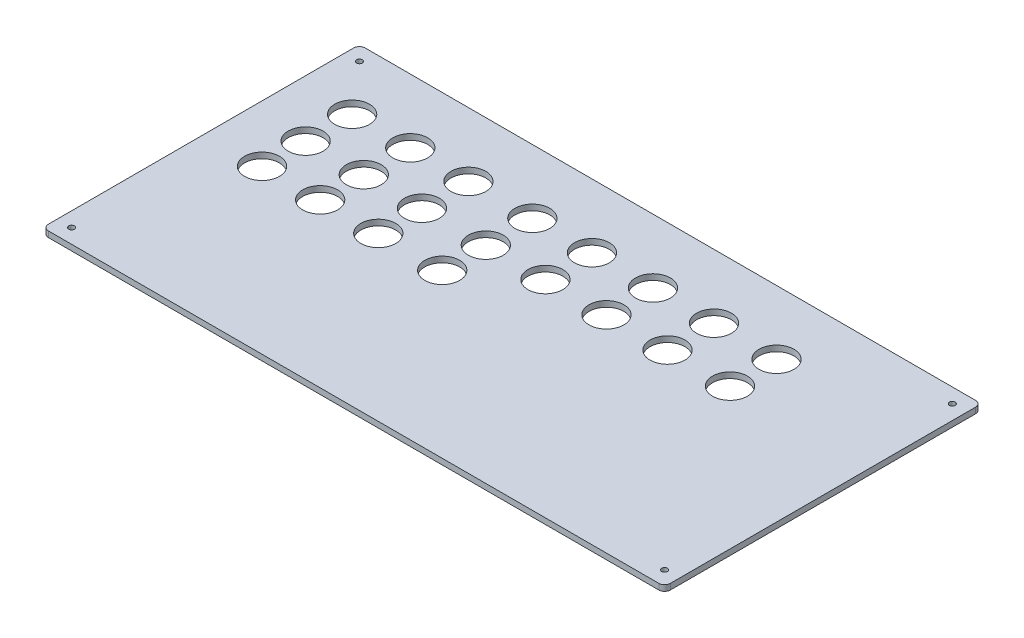
SolidWorks part; units mm, degrees
ref_plane "Front Plane" through (0, 0, 0) normal (0, 0, 1) x (1, 0, 0)
ref_plane "Top Plane" through (0, 0, 0) normal (0, 1, 0) x (1, 0, 0)
ref_plane "Right Plane" through (0, 0, 0) normal (1, 0, 0) x (0, 0, -1)
sketch "Sketch2" plane through (0, 0, 0) normal (0, 1, 0) x (1, 0, 0)
  line L1 (105, 54.5) -> (-105, 54.5)
  line L2 (107, 52.5) -> (107, -52.5)
  line L3 (105, -54.5) -> (-105, -54.5)
  line L4 (-107, 52.5) -> (-107, -52.5)
  line L5 (107, 54.5) -> (-107, -54.5) construction
  line L6 (107, -54.5) -> (-107, 54.5) construction
  arc A0 (105, 54.5) -> (107, 52.5) centre (105, 52.5) cw
  arc A1 (107, -52.5) -> (105, -54.5) centre (105, -52.5) cw
  arc A2 (-105, -54.5) -> (-107, -52.5) centre (-105, -52.5) cw
  arc A3 (-105, 54.5) -> (-107, 52.5) centre (-105, 52.5) ccw
  point P0 (0, 0)
  dimension "D3" = 2
  dimension "D1" = 214
  dimension "D2" = 109
extrude "Boss-Extrude1" add sketch "Sketch2" along normal blind 2
sketch "Sketch3" plane through (0, 2, 0) normal (0, 1, 0) x (1, 0, 0)
  line L0 (-107, 52.5) -> (-107, -52.5) construction
  line L1 (105, 54.5) -> (-105, 54.5) construction
  circle A0 centre (-87.5, 32.5) radius 6
  circle A1 centre (-67.5, 32.5) radius 6
  circle A2 centre (-47.5, 32.5) radius 6
  circle A3 centre (-25.5, 32.5) radius 6
  circle A4 centre (-5, 32.5) radius 6
  circle A5 centre (16, 32.5) radius 6
  circle A6 centre (37, 32.5) radius 6
  circle A7 centre (58.5, 32.5) radius 6
  circle A8 centre (-87.5, 16.5) radius 6
  circle A9 centre (-67.5, 16.5) radius 6
  circle A10 centre (-47.5, 16.5) radius 6
  circle A11 centre (-25.5, 16.5) radius 6
  circle A12 centre (-5, 16.5) radius 6
  circle A13 centre (16, 16.5) radius 6
  circle A14 centre (37, 16.5) radius 6
  circle A15 centre (58.5, 16.5) radius 6
  circle A16 centre (-67.5, 1.5) radius 6
  circle A17 centre (-87.5, 1.5) radius 6
  circle A18 centre (-47.5, 1.5) radius 6
  circle A19 centre (-25.5, 1.5) radius 6
  dimension "D3" = 12
  dimension "D8" = 2
  dimension "D1" = 19.5
  dimension "D2" = 22
  dimension "D5" = 20
  dimension "D7" = 22
  dimension "D9" = 20.5
  dimension "D11" = 21
  dimension "D13" = 21.5
  dimension "D15" = 16
  dimension "D17" = 15
  dimension "D4" = 3
  dimension "D6" = 2
  dimension "D10" = 3
  dimension "D12" = 2
  dimension "D14" = 2
  dimension "D16" = 2
extrude "Cut-Extrude1" cut sketch "Sketch3" against normal blind 3
hole_wizard "Ø2.0mm Dowel Hole1" positions "Sketch4" profile "Sketch5" hole size "Ø2.0" standard "ANSI Metric"
sketch "Sketch4" plane through (0, 2, 0) normal (0, 1, 0) x (1, 0, 0)
  line L0 (105, 54.5) -> (-105, 54.5) construction
  line L1 (-107, 52.5) -> (-107, -52.5) construction
  line L2 (107, -52.5) -> (107, 52.5) construction
  line L3 (-105, -54.5) -> (105, -54.5) construction
  point P0 (-102, 49.5)
  point P2 (102, 49.5)
  point P4 (102, -49.5)
  point P6 (-102, -49.5)
  dimension "D1" = 5
  dimension "D2" = 5
  dimension "D3" = 5
  dimension "D4" = 5
  dimension "D5" = 5
  dimension "D6" = 5
  dimension "D7" = 5
  dimension "D8" = 5
sketch "Sketch5" plane through (-102, 2, -49.5) normal (1, 0, 0) x (0, 0, 1)
  line L0 (0, 0) -> (0, 8.6009)
  line L1 (0, 8.6009) -> (1, 8)
  line L2 (1, 8) -> (1, 0)
  line L5 (1, 0) -> (0, 0)
  line L10 (0, 8.6009) -> (-1, 8) construction
  line L11 (0, -6.35) -> (0, 107.95) construction
  dimension "Hole Dia." = 2
  dimension "Hole Depth" = 8
  dimension "Drill Angle" = 118
